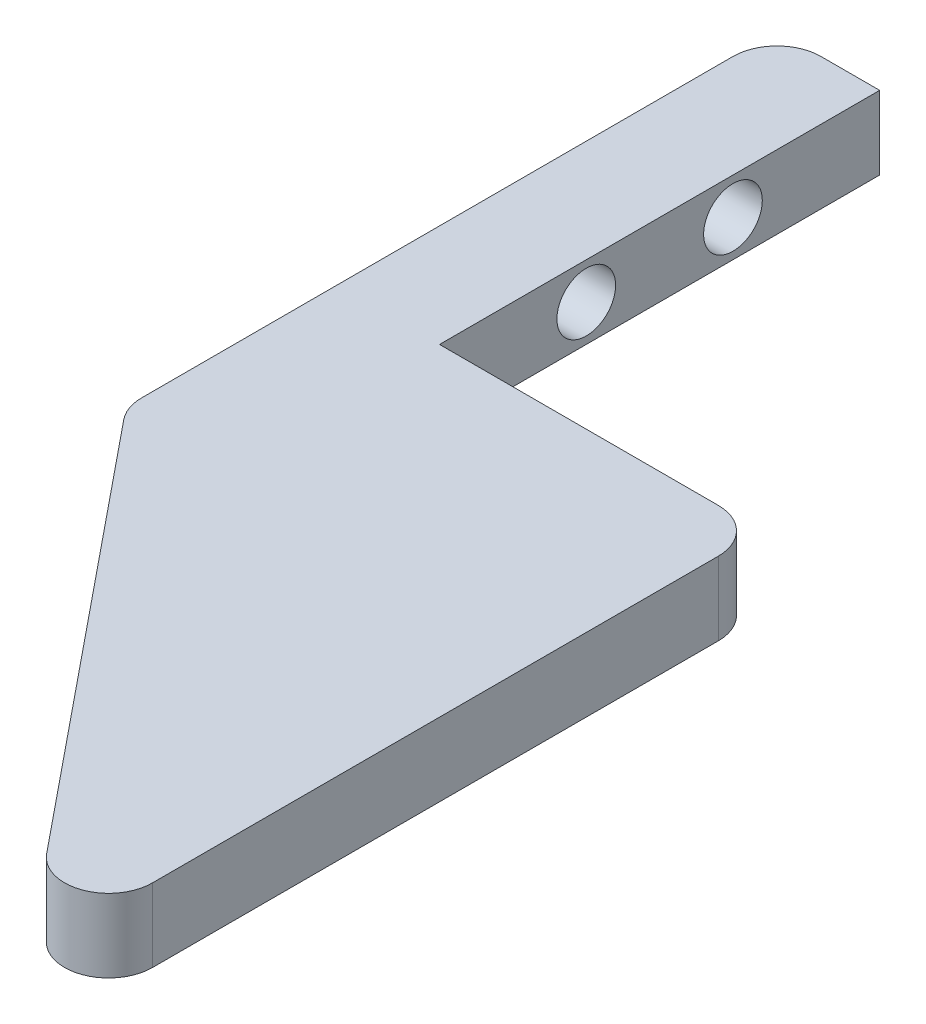
SolidWorks part; units mm, degrees
ref_plane "Front Plane" through (0, 0, 0) normal (0, 0, 1) x (1, 0, 0)
ref_plane "Top Plane" through (0, 0, 0) normal (0, 1, 0) x (1, 0, 0)
ref_plane "Right Plane" through (0, 0, 0) normal (1, 0, 0) x (0, 0, -1)
sketch "Sketch1" plane through (0, 0, 0) normal (0, 1, 0) x (1, 0, 0)
  line L0 (2.3649, -62.7232) -> (-26.6351, -27.0941)
  line L5 (2.3649, -12.7232) -> (2.3649, -62.7232)
  line L6 (-26.6351, -27.0941) -> (-26.6351, 17.2768)
  line L15 (-26.6351, 17.2768) -> (-19.6351, 17.2768)
  line L16 (-19.6351, 17.2768) -> (-19.6351, -12.7232)
  line L17 (-19.6351, -12.7232) -> (2.3649, -12.7232)
  point P0 (0, 0)
  dimension "D1" = 22
  dimension "D2" = 7
extrude "Boss-Extrude1" add sketch "Sketch1" along normal blind 5
sketch "Sketch3" plane through (-19.6351, 0, 0) normal (1, 0, 0) x (0, 0, -1)
  line L0 (-12.7232, 0) -> (17.2768, 0) construction
  line L1 (17.2768, 5) -> (17.2768, 0) construction
  circle A0 centre (-2.7232, 2.5) radius 2
  circle A1 centre (7.2768, 2.5) radius 2
  dimension "D1" = 4
  dimension "D2" = 4
  dimension "D3" = 2.5
  dimension "D4" = 2.5
  dimension "D5" = 10
  dimension "D6" = 10
extrude "Cut-Extrude2" cut sketch "Sketch3" against normal blind 20
fillet "Fillet2" radius 3 1 edges at (2.3649, 2.5, 62.7232)
fillet "Fillet3" radius 3 2 edges at (2.3649, 2.5, 12.7232) (-26.6351, 2.5, -17.2768)
fillet "Fillet4" radius 3 1 edges at (-26.6351, 2.5, 27.0941)
